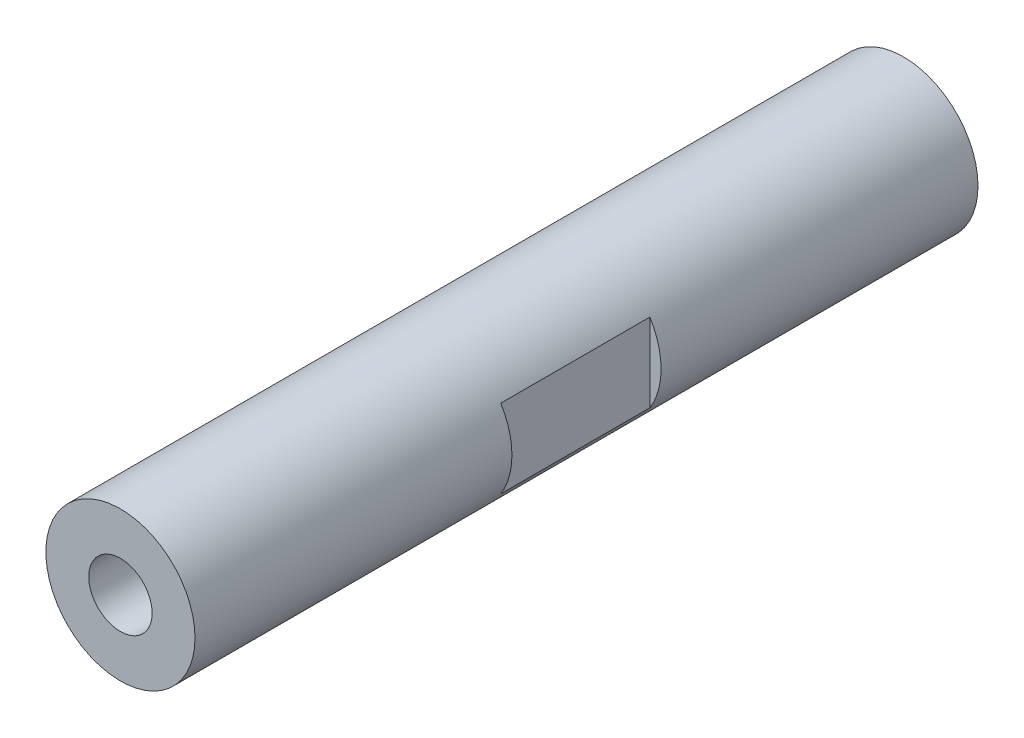
SolidWorks part; units mm, degrees
ref_plane "前视基准面" through (0, 0, 0) normal (0, 0, 1) x (1, 0, 0)
ref_plane "上视基准面" through (0, 0, 0) normal (0, 1, 0) x (1, 0, 0)
ref_plane "右视基准面" through (0, 0, 0) normal (1, 0, 0) x (0, 0, -1)
sketch "草图1" plane through (0, 0, 0) normal (0, 0, 1) x (1, 0, 0)
  circle A0 centre (0, 0) radius 10
  dimension "D1" = 20
extrude "凸台-拉伸1" add sketch "草图1" along normal mid plane 105
sketch "草图2" plane through (0, 0, 0) normal (0, 1, 0) x (1, 0, 0)
  line L0 (-10, 52.5) -> (-10, -52.5) construction
  line L1 (-8.5, -10) -> (-11.5, -10)
  line L2 (-8.5, -10) -> (-8.5, 10)
  line L3 (-8.5, 10) -> (-11.5, 10)
  line L4 (-11.5, -10) -> (-11.5, 10)
  line L5 (-8.5, -10) -> (-11.5, 10) construction
  line L6 (-8.5, 10) -> (-11.5, -10) construction
  line L7 (0, 0) -> (0, 9.4983) construction
  line L8 (8.5, 10) -> (11.5, -10) construction
  line L9 (8.5, -10) -> (11.5, 10) construction
  line L10 (11.5, -10) -> (11.5, 10)
  line L11 (8.5, 10) -> (11.5, 10)
  line L12 (8.5, -10) -> (8.5, 10)
  line L13 (8.5, -10) -> (11.5, -10)
  point P0 (-10, 0)
  point P14 (10, 0)
  dimension "D1" = 17
  dimension "D2" = 20
extrude "切除-拉伸1" cut sketch "草图2" against normal mid plane 60
sketch "草图3" plane through (0, 0, 52.5) normal (0, 0, 1) x (1, 0, 0)
  circle A0 centre (0, 0) radius 3.0089
hole_wizard "M10 螺纹孔1" positions "3D草图1" profile "草图4" tap size "M10" standard "Ks"
sketch3d "3D草图1"
  point P0 (0, 0, 52.5)
sketch "草图4" plane through (0, 0, 52.5) normal (1, 0, 0) x (0, -1, 0)
  line L0 (0, 0) -> (0, 27.0537)
  line L1 (0, 27.0537) -> (4.25, 24.5)
  line L2 (4.25, 24.5) -> (4.25, 0)
  line L5 (4.25, 0) -> (0, 0)
  line L10 (0, 27.0537) -> (-4.25, 24.5) construction
  line L11 (0, -6.35) -> (0, 107.95) construction
  dimension "螺纹孔钻头直径" = 8.5
  dimension "螺纹孔钻头深度" = 24.5
  dimension "导头角度" = 118
mirror "镜向1" about plane through (0, 0, 0) normal (0, 0, 1) of "M10 螺纹孔1"
